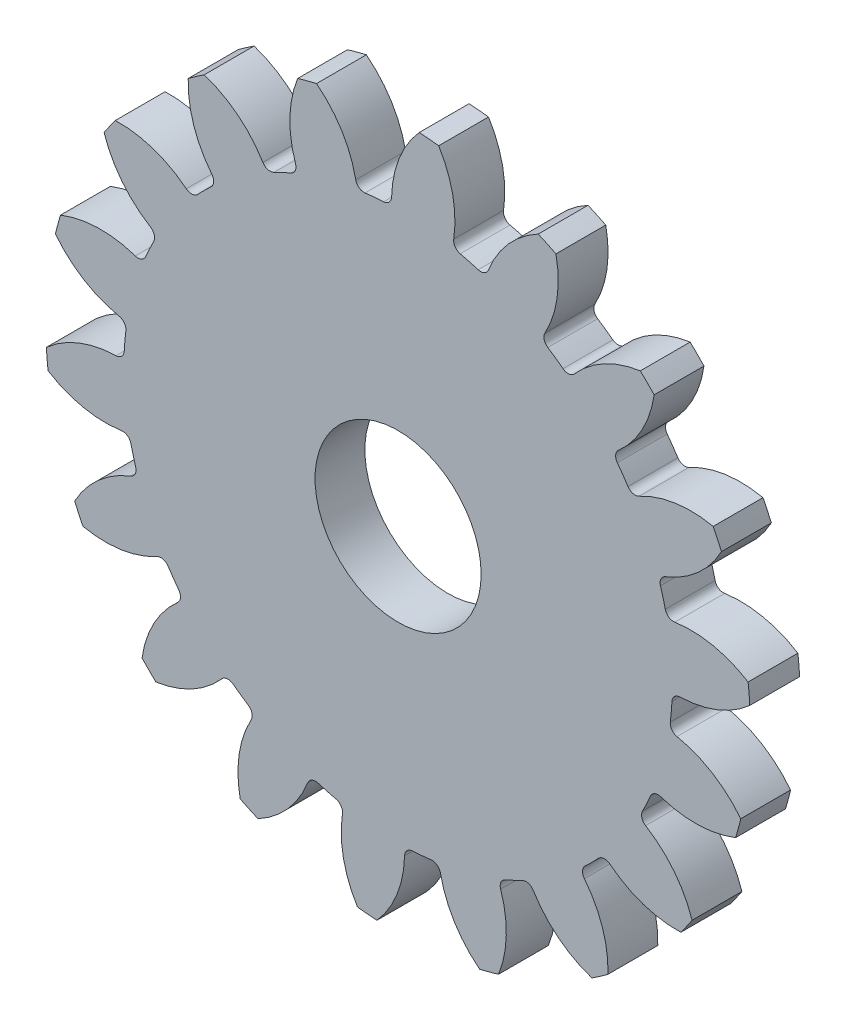
SolidWorks part; units mm, degrees
ref_plane "Alzado" through (0, 0, 0) normal (0, 0, 1) x (1, 0, 0)
ref_plane "Planta" through (0, 0, 0) normal (0, 1, 0) x (1, 0, 0)
ref_plane "Vista lateral" through (0, 0, 0) normal (1, 0, 0) x (0, 0, -1)
sketch "Croquis1" plane through (0, 0, 0) normal (0, 0, 1) x (1, 0, 0)
  circle A0 centre (0, 0) radius 21.209
  dimension "D1" = 42.418
extrude "Saliente-Extruir1" add sketch "Croquis1" along normal blind 3
sketch "Croquis2" plane through (0, 0, 3) normal (0, 0, 1) x (1, 0, 0)
  line L0 (0, 0) -> (0, 19.05) construction
  line L1 (0, 0) -> (7.8242, 21.4969) construction
  line L2 (0, 0) -> (-1.651, 18.9783) construction
  line L3 (0, 19.05) -> (6.1226, 16.8216) construction
  arc A0 (1.2712, 21.1709) -> (-4.908, 20.6333) centre (0, 0) ccw
  arc A2 (-0.3853, 16.5055) -> (-2.4707, 16.3241) centre (0, 0) ccw
  arc A3 (1.2712, 21.1709) -> (-0.3853, 16.5055) centre (6.1226, 16.8216) ccw
  arc A4 (-4.908, 20.6333) -> (-2.4707, 16.3241) centre (-8.9353, 15.5116) cw
  dimension "D2" = 33.02
  dimension "D3" = 20
  dimension "D4" = 1.651
extrude "Cortar-Extruir1" cut sketch "Croquis2" against normal through all
fillet "Redondeo1" radius 0.508 2 edges at (-0.3853, 16.5055, 1.5) (-2.4707, 16.3241, 1.5)
pattern_circular "MatrizC1" count 18 over 360 about axis through (0, 0, 0) along (0, 0, 1) of "Redondeo1", "Cortar-Extruir1"
sketch "Croquis3" plane through (0, 0, 3) normal (0, 0, 1) x (1, 0, 0)
  circle A0 centre (0, 0) radius 5
  dimension "D1" = 10
extrude "Cortar-Extruir2" cut sketch "Croquis3" against normal through all
